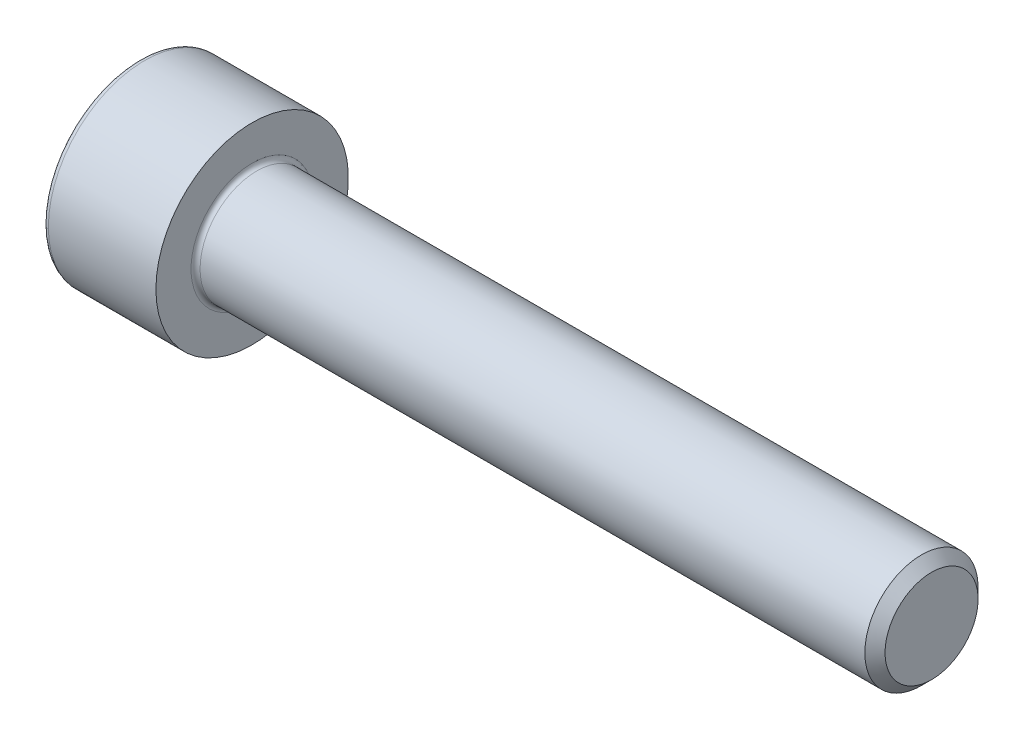
SolidWorks part; units mm, degrees
revolve "Base-Revolve" add sketch "BodySke"
sketch "BodySke" plane through (0, 0, 0) normal (0, 0, 1) x (1, 0, 0)
  line L0 (0, 0) -> (0, 4.25)
  line L1 (0, 4.25) -> (5, 4.25)
  line L2 (5, 4.25) -> (5, 2.5)
  line L3 (5, 2.5) -> (34.555, 2.5)
  line L4 (35, 2.055) -> (35, 0)
  line L5 (35, 0) -> (0, 0)
  line L6 (-31.75, 0) -> (127, 0) construction
  line L8 (35, 2.055) -> (34.555, 2.5)
  line L10 (35, -2.055) -> (34.555, -2.5) construction
  line L11 (5.8, 9.525) -> (5.8, 3.175) construction
  line L12 (13, 9.525) -> (13, 3.175) construction
  line L13 (-25, 9.525) -> (-25, 3.175) construction
  dimension "Head_ht" = 5
  dimension "Length" = 30
  dimension "Body_ch_ang" = 45
  dimension "Diameter" = 5
  dimension "Minor_dia" = 4.11
  dimension "Advance" = 0.8
  dimension "Thread_nom" = 22
  dimension "Thread_length" = 60
  dimension "Head_dia" = 8.5
cosmetic thread "ThreadCosmetic" [suppressed]
fillet "Fillet1" radius 0.2 1 edges at (5, 0, 2.5)
fillet "Fillet2" radius 0.25 1 edges at (0, 0, 4.25)
material "AISI 304"
ref_plane "Plane1" through (0, 0, 0) normal (0, 0, 1) x (1, 0, 0)
ref_plane "Plane2" through (0, 0, 0) normal (0, 1, 0) x (1, 0, 0)
ref_plane "Plane3" through (0, 0, 0) normal (1, 0, 0) x (0, 0, -1)
other "Configuration Table"
sketch "Sketch2" plane through (0, 0, 0) normal (0, 0, 1) x (1, 0, 0)
  line L0 (0, 2.042) -> (2.5, 2.042)
  line L1 (2.5, 2.042) -> (3.6789, 0)
  line L2 (-31.75, 0) -> (127, 0) construction
  line L3 (3.6789, 0) -> (0, 0)
  line L4 (0, 0) -> (0, 2.042)
  line L6 (0, 0) -> (47.625, 0) construction
  dimension "D1" = 2.042
  dimension "D2" = 60
  dimension "Depth" = 2.5
revolve "Hex-PreBroach" cut sketch "Sketch2" angle 360 about L6
sketch "Sketch3" plane through (0, 0, 0) normal (-1, 0, 0) x (0, 0.5, 0.866)
  line L0 (1.1789, 2.042) -> (-1.1789, 2.042)
  line L1 (-1.1789, 2.042) -> (-2.3579, 0)
  line L2 (1.1789, 2.042) -> (2.3579, 0)
  line L3 (1.1789, -2.042) -> (2.3579, 0)
  line L4 (1.1789, -2.042) -> (-1.1789, -2.042)
  line L5 (-1.1789, -2.042) -> (-2.3579, 0)
  dimension "D1" = 2.042
  dimension "D2" = 2.042
  dimension "Hex_size" = 4.084
extrude "Hex" cut sketch "Sketch3" against normal blind 2.5
sketch "ThdSchSke" plane through (0, 0, 0) normal (0, 0, 1) x (1, 0, 0)
  line L0 (13, -2.055) -> (12.6884, -2.5)
  line L1 (13, -2.055) -> (13.3116, -2.5)
  line L2 (13.3116, -2.5) -> (13.3116, -3.125)
  line L3 (-3.175, 0) -> (5.1513, 0) construction
  line L4 (0, 4) -> (0, -4) construction
  line L5 (13.3116, -3.125) -> (12.6884, -3.125)
  line L6 (12.6884, -3.125) -> (12.6884, -2.5)
  dimension "Thread_minor" = 4.11
  dimension "Diameter" = 5
  dimension "Start" = 13
revolve "ThreadSchematic" [suppressed] cut sketch "ThdSchSke" angle 360 about L3
pattern_linear "ThdSchPat" [suppressed]
equation "\"D2@Sketch3\" = \"Hex_size@Sketch3\" / 2"
equation "\"D1@Sketch3\" = \"Hex_size@Sketch3\" / 2"
equation "\"D1@Sketch2\" = \"Hex_size@Sketch3\" / 2"
equation "\"Thread_minor@ThreadCosmetic\"  =  \"Minor_dia@BodySke\""
equation "\"Depth@Sketch2\" =  \"Key_eng@Hex\""
equation "\"Thread_length@ThreadCosmetic\" = ((sgn( (\"Length@BodySke\" - \"Advance@BodySke\" * 3.0) - \"Thread_nom@BodySke\" )-1)*( (\"Length@BodySke\" - \"Advance@BodySke\" * 3.0) - \"Thread_nom@BodySke\" ))/-2+ \"Thread_nom@BodySke\""
equation "\"Thread_minor@ThdSchSke\" = \"Minor_dia@BodySke\""
equation "\"Diameter@ThdSchSke\" = \"Diameter@BodySke\""
equation "\"Overcut@ThdSchSke\" = \"Diameter@BodySke\" * 1.25"
equation "\"Start@ThdSchSke\" = \"Head_ht@BodySke\" + \"Length@BodySke\" - \"Thread_length@ThreadCosmetic\"  '---Non-countersunk---"
equation "\"Num_threads@ThdSchPat\" = int( \"Thread_length@ThreadCosmetic\" / \"Advance@BodySke\" + 0.999 )  + 1"
equation "\"Advance@ThdSchPat\" = \"Thread_length@ThreadCosmetic\" /  (\"Num_threads@ThdSchPat\" - 1) 'relax it"
equation "\"Num_threads@ThdSchPat\" = \"Num_threads@ThdSchPat\" - sgn( \"Num_threads@ThdSchPat\" - 1) '---chamfered tips only---"
